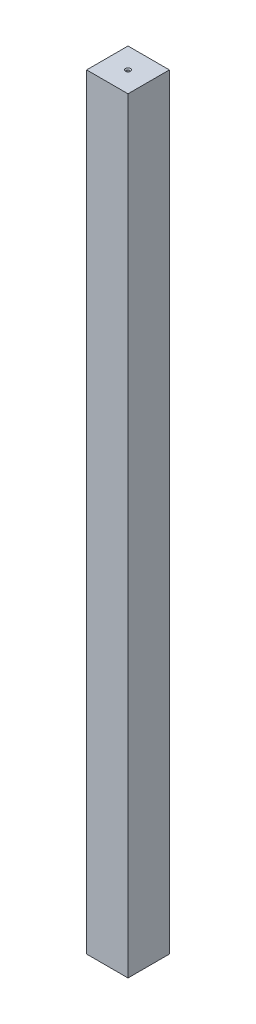
SolidWorks part; units mm, degrees
material "Balsa"
ref_plane "Front Plane" through (0, 0, 0) normal (0, 0, 1) x (1, 0, 0)
ref_plane "Top Plane" through (0, 0, 0) normal (0, 1, 0) x (1, 0, 0)
ref_plane "Right Plane" through (0, 0, 0) normal (1, 0, 0) x (0, 0, -1)
sketch "Sketch1" plane through (0, 0, 0) normal (0, 1, 0) x (1, 0, 0)
  line L1 (-12.7, 12.7) -> (12.7, 12.7)
  line L2 (-12.7, 12.7) -> (-12.7, -12.7)
  line L3 (-12.7, -12.7) -> (12.7, -12.7)
  line L4 (12.7, 12.7) -> (12.7, -12.7)
  line L5 (-12.7, 12.7) -> (12.7, -12.7) construction
  line L6 (-12.7, -12.7) -> (12.7, 12.7) construction
  point P0 (0, 0)
  dimension "D1" = 25.4
  dimension "D2" = 25.4
extrude "Boss-Extrude1" add sketch "Sketch1" along normal mid plane 470
hole_wizard "CSK for #0 Flat Head Machine Screw (100)1" positions "Sketch2" profile "Sketch3" countersink size "#0" standard "ANSI Inch"
sketch "Sketch2" plane through (0, 235, 0) normal (0, 1, 0) x (1, 0, 0)
  point P0 (0, 0)
sketch "Sketch3" plane through (0, 235, 0) normal (1, 0, 0) x (0, 0, 1)
  line L0 (0, 0) -> (0, 32.2346)
  line L1 (0, 32.2346) -> (0.8064, 31.75)
  line L2 (0.8064, 31.75) -> (0.8064, 0.5914)
  line L3 (0.8064, 0.5914) -> (1.5113, 0)
  line L5 (1.5113, 0) -> (0, 0)
  line L6 (-0.8064, 0.5914) -> (-1.5113, 0) construction
  line L10 (0, 32.2346) -> (-0.8065, 31.75) construction
  line L11 (0, -6.35) -> (0, 107.95) construction
  dimension "Hole Dia." = 1.6129
  dimension "Hole Depth" = 31.75
  dimension "Near C'Sink Dia." = 3.0226
  dimension "Near C'Sink Angle" = 100
  dimension "Drill Angle" = 118
mirror "Mirror1" about plane through (0, 0, 0) normal (0, 1, 0) of "CSK for #0 Flat Head Machine Screw (100)1"
